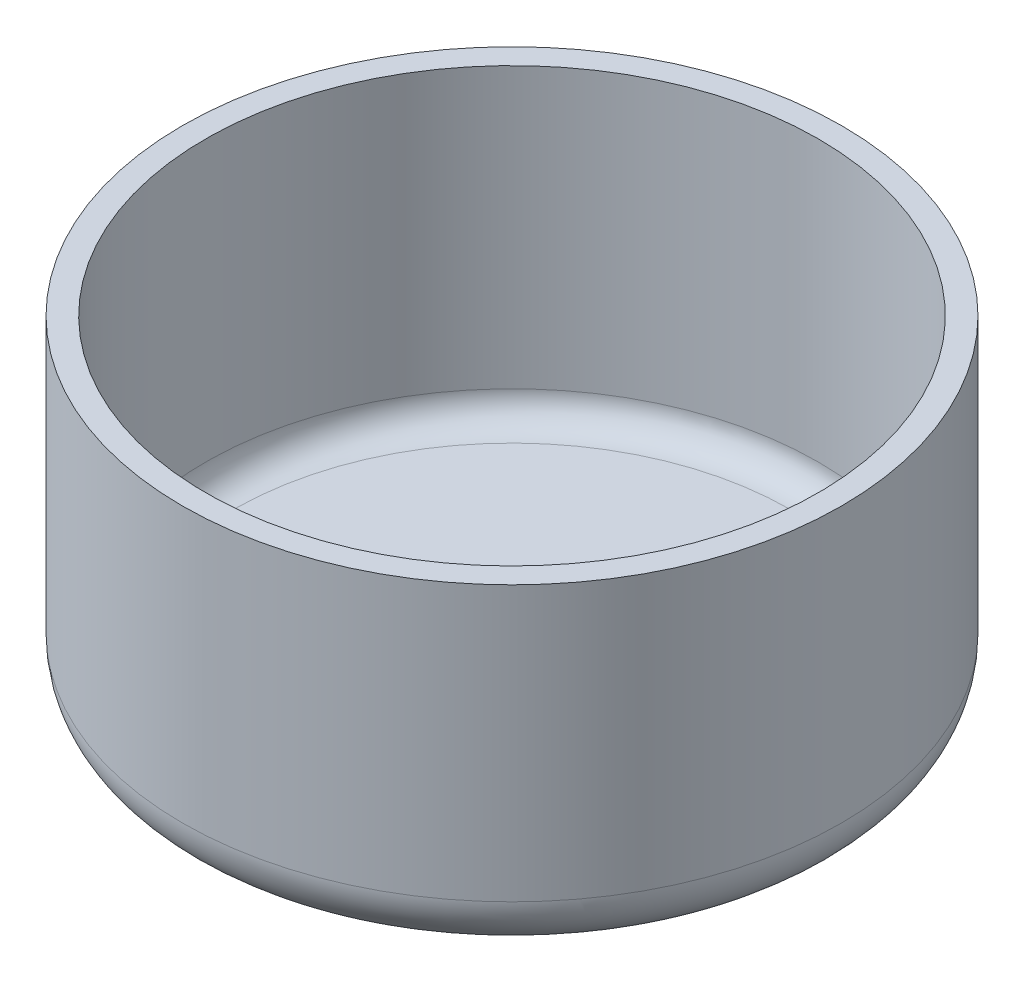
SolidWorks part; units mm, degrees
material "Copper"
ref_plane "Front Plane" through (0, 0, 0) normal (0, 0, 1) x (1, 0, 0)
ref_plane "Top Plane" through (0, 0, 0) normal (0, 1, 0) x (1, 0, 0)
ref_plane "Right Plane" through (0, 0, 0) normal (1, 0, 0) x (0, 0, -1)
sketch "Sketch1" plane through (0, 0, 0) normal (0, 0, 1) x (1, 0, 0)
  line L0 (3.302, 0) -> (9.9314, 0)
  line L1 (11.9634, 2.032) -> (11.9634, 12)
  line L2 (0, 0) -> (0, 16.4584) construction
  line L3 (11.1252, 12) -> (11.9634, 12)
  line L4 (3.302, 0) -> (3.302, 0.8382)
  line L5 (3.302, 0.8382) -> (10.1252, 0.8382)
  line L6 (11.1252, 1.8382) -> (11.1252, 12)
  arc A0 (9.9314, 0) -> (11.9634, 2.032) centre (9.9314, 2.032) ccw
  arc A1 (10.1252, 0.8382) -> (11.1252, 1.8382) centre (10.1252, 1.8382) ccw
  dimension "D1" = 2.032
  dimension "D5" = 1
  dimension "D2" = 3.302
  dimension "D3" = 12
  dimension "D4" = 11.9634
  dimension "D6" = 0.8382
  dimension "D7" = 0.8382
revolve "Revolve1" add sketch "Sketch1" angle 360 about L2
sketch "Sketch2" plane through (0, 0, 0) normal (0, 0, 1) x (1, 0, 0)
  line L0 (0, 2.032) -> (0, 0) construction
  line L1 (-0.7938, 12.7727) -> (0.7937, 12.7727)
  line L2 (-0.7938, 12.7727) -> (-0.7937, 2.032)
  line L3 (-0.7937, 2.032) -> (0.7937, 2.032)
  line L4 (0.7937, 12.7727) -> (0.7937, 2.032)
  line L5 (11.9634, 2.032) -> (-11.9634, 2.032) construction
  dimension "D1" = 1.5875
extrude "Cut-Extrude1" [suppressed] cut sketch "Sketch2" against normal through all
pattern_circular "CirPattern1" [suppressed] count 12 over 360
